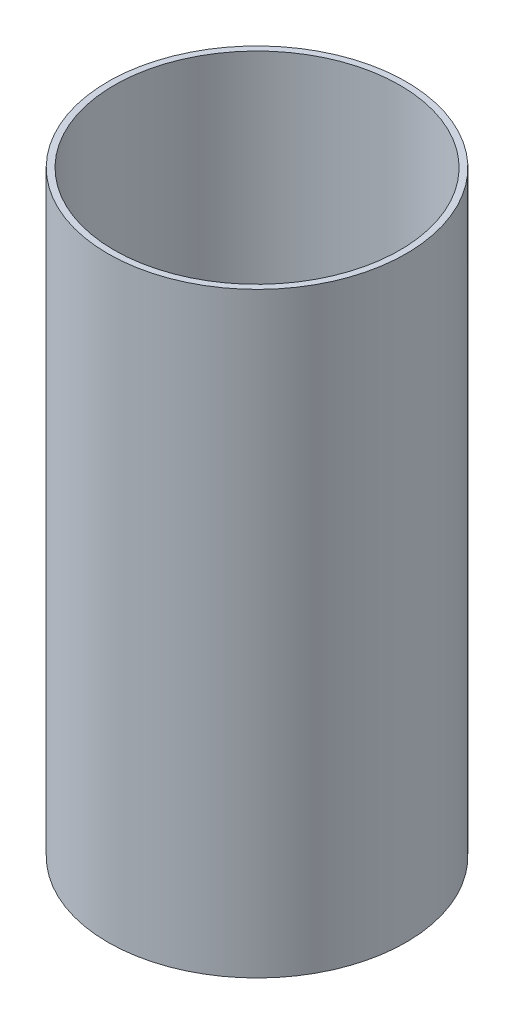
SolidWorks part; units mm, degrees
material "G10 Fiberglass"
ref_plane "Front Plane" through (0, 0, 0) normal (0, 0, 1) x (1, 0, 0)
ref_plane "Top Plane" through (0, 0, 0) normal (0, 1, 0) x (1, 0, 0)
ref_plane "Right Plane" through (0, 0, 0) normal (1, 0, 0) x (0, 0, -1)
sketch "Sketch1" plane through (0, 0, 0) normal (0, 1, 0) x (1, 0, 0)
  circle A0 centre (0, 0) radius 76.2
  circle A1 centre (0, 0) radius 73.025
  dimension "D1" = 152.4
  dimension "D2" = 146.05
extrude "Boss-Extrude1" add sketch "Sketch1" along normal blind 304.8
